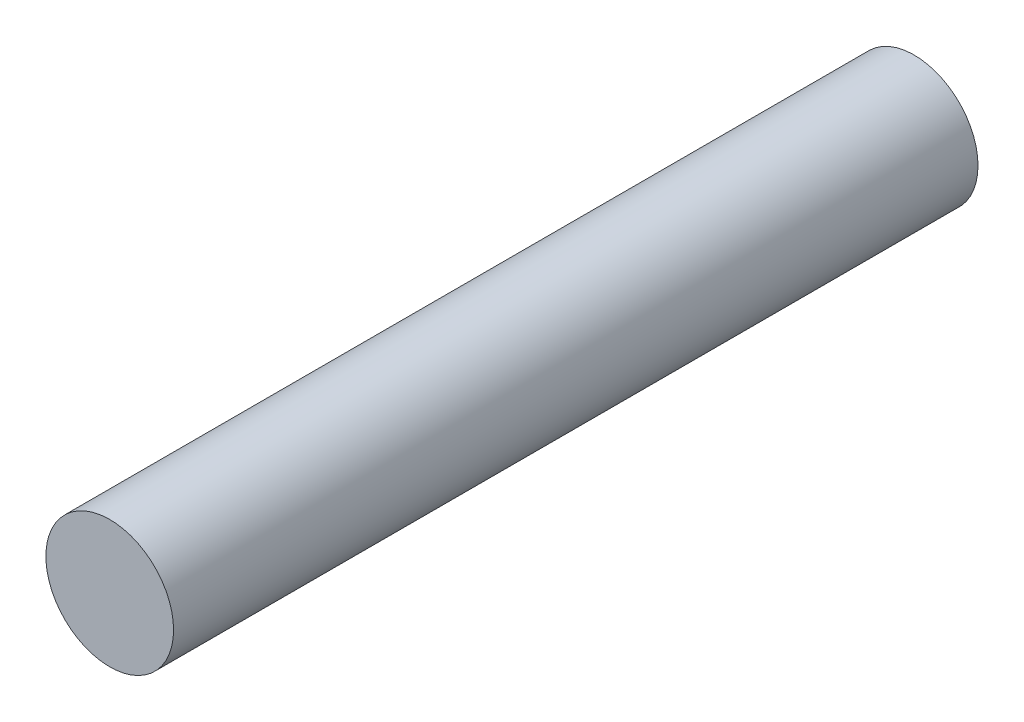
SolidWorks part; units mm, degrees
ref_plane "Front Plane" through (0, 0, 0) normal (0, 0, 1) x (1, 0, 0)
ref_plane "Top Plane" through (0, 0, 0) normal (0, 1, 0) x (1, 0, 0)
ref_plane "Right Plane" through (0, 0, 0) normal (1, 0, 0) x (0, 0, -1)
sketch "Sketch1" plane through (0, 0, 0) normal (0, 0, 1) x (1, 0, 0)
  circle A0 centre (0, 0) radius 5
  dimension "D1" = 10
extrude "Boss-Extrude1" add sketch "Sketch1" along normal blind 63
